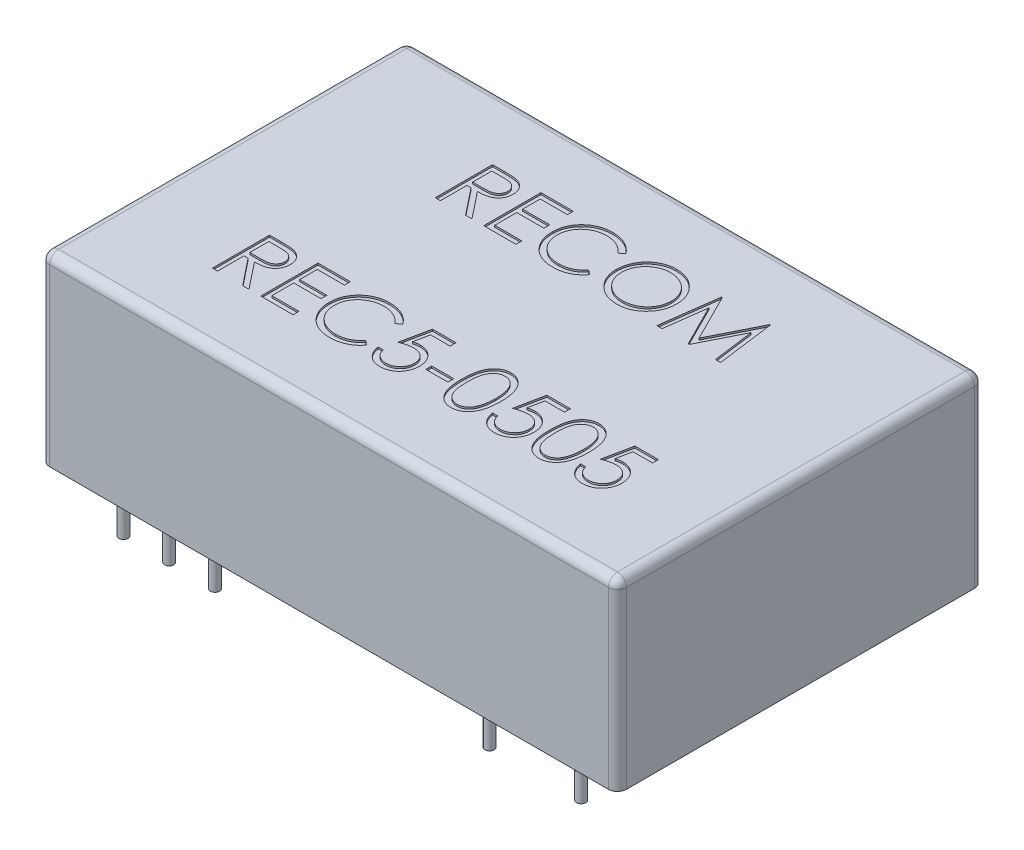
SolidWorks part; units mm, degrees
ref_plane "Front Plane" through (0, 0, 0) normal (0, 0, 1) x (1, 0, 0)
ref_plane "Top Plane" through (0, 0, 0) normal (0, 1, 0) x (1, 0, 0)
ref_plane "Right Plane" through (0, 0, 0) normal (1, 0, 0) x (0, 0, -1)
sketch "Sketch1" plane through (0, 0, 0) normal (0, 1, 0) x (1, 0, 0)
  line L1 (-16, 10.15) -> (16, 10.15)
  line L2 (-16, 10.15) -> (-16, -10.15)
  line L3 (-16, -10.15) -> (16, -10.15)
  line L4 (16, 10.15) -> (16, -10.15)
  line L5 (-16, 10.15) -> (16, -10.15) construction
  line L6 (-16, -10.15) -> (16, 10.15) construction
  point P0 (0, 0)
  dimension "D1" = 32
  dimension "D2" = 20.3
extrude "Boss-Extrude1" add sketch "Sketch1" along normal blind 10.2
sketch "Sketch2" plane through (0, 0, 0) normal (0, -1, 0) x (1, 0, 0)
  line L0 (-16, 7.62) -> (16, 7.62) construction
  line L1 (-16, -7.62) -> (16, -7.62) construction
  line L2 (-16, -10.15) -> (-16, 10.15) construction
  line L3 (16, 10.15) -> (16, -10.15) construction
  line L4 (-11.4, 7.62) -> (-11.4, -7.62) construction
  line L5 (-8.86, 7.62) -> (-8.86, -7.62) construction
  line L6 (6.38, 7.62) -> (6.38, -7.62) construction
  line L7 (11.46, 7.62) -> (11.46, -7.62) construction
  line L8 (-16, 0) -> (16, 0) construction
  line L9 (-4.5655, 7.62) -> (-4.5655, 0) construction
  line L10 (-4.5655, 0) -> (-4.5655, -7.62) construction
  circle A0 centre (-13.94, 7.62) radius 0.255
  circle A1 centre (-11.4, 7.62) radius 0.255
  circle A2 centre (-8.86, 7.62) radius 0.255
  circle A3 centre (6.38, 7.62) radius 0.255
  circle A4 centre (11.46, 7.62) radius 0.255
  circle A5 centre (-11.4, -7.62) radius 0.255
  circle A6 centre (-8.86, -7.62) radius 0.255
  circle A7 centre (6.38, -7.62) radius 0.255
  circle A8 centre (11.46, -7.62) radius 0.255
  point P28 (-11.4, 0)
  dimension "D1" = 0.51
  dimension "D2" = 2.54
  dimension "D3" = 2.54
  dimension "D4" = 15.24
  dimension "D5" = 5.08
  dimension "D6" = 4.6
  dimension "D7" = 15.24
extrude "Boss-Extrude2" add sketch "Sketch2" along normal blind 3.8
fillet "Fillet1" radius 0.5 8 edges at (0, 10.2, -10.15) (-16, 5.1, -10.15) (-16, 10.2, 0) (0, 10.2, 10.15) (16, 10.2, 0) (16, 5.1, -10.15) (16, 5.1, 10.15) (-16, 5.1, 10.15)
sketch "Sketch3" plane through (0, 10.2, 0) normal (0, 1, 0) x (1, 0, 0)
  text T0 "RECOM"
  text T1 "REC5-0505"
extrude "Cut-Extrude1" cut sketch "Sketch3" against normal blind 0.1
